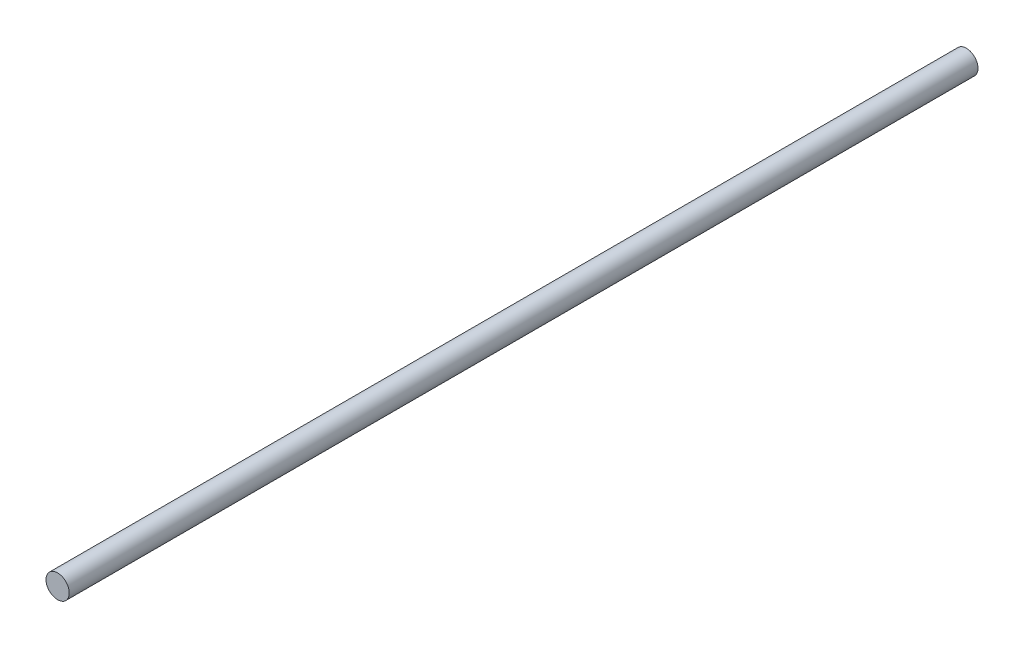
SolidWorks part; units mm, degrees
ref_plane "Front" through (0, 0, 0) normal (0, 0, 1) x (1, 0, 0)
ref_plane "Top" through (0, 0, 0) normal (0, 1, 0) x (1, 0, 0)
ref_plane "Right" through (0, 0, 0) normal (1, 0, 0) x (0, 0, -1)
sketch "Sketch1" plane through (0, 0, 0) normal (0, 0, 1) x (1, 0, 0)
  circle A0 centre (0, 0) radius 4
  dimension "D1" = 8
extrude "Boss-Extrude1" add sketch "Sketch1" along normal blind 312.45
